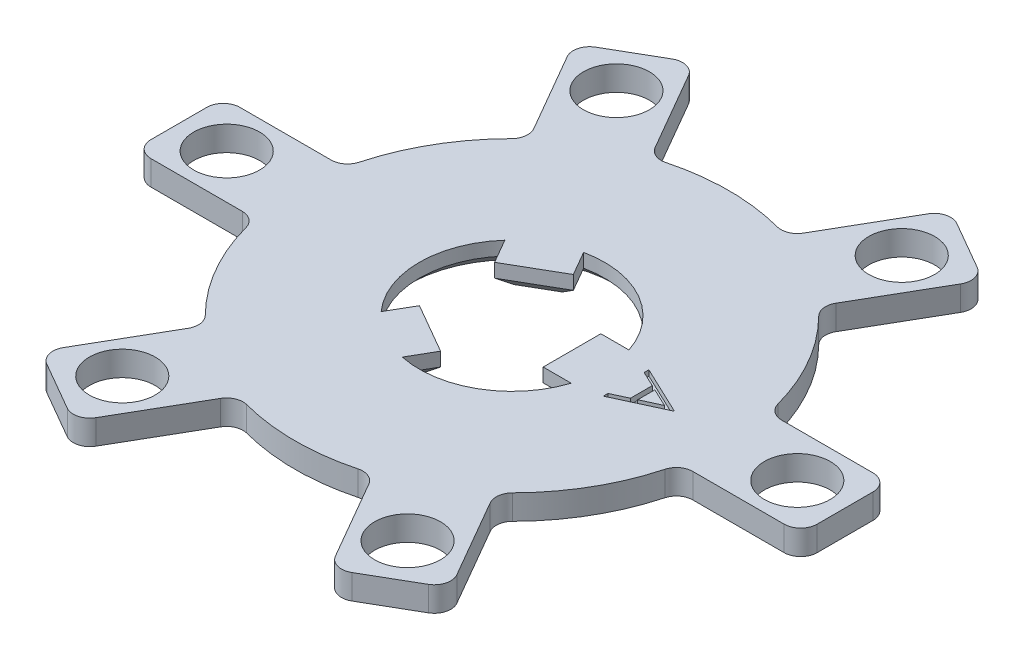
SolidWorks part; units mm, degrees
ref_plane "Front Plane" through (0, 0, 0) normal (0, 0, 1) x (1, 0, 0)
ref_plane "Top Plane" through (0, 0, 0) normal (0, 1, 0) x (1, 0, 0)
ref_plane "Right Plane" through (0, 0, 0) normal (1, 0, 0) x (0, 0, -1)
sketch "Sketch1" plane through (0, 0, 0) normal (0, 1, 0) x (1, 0, 0)
  line L0 (0, -15.8) -> (0, 15.8) construction
  line L1 (-15.8, 0) -> (0, 0) construction
  line L18 (-15.8, 0) -> (15.8, 0) construction
  line L23 (26.5479, 0) -> (-28.3106, 0) construction
  line L24 (4.9298, -15.0112) -> (9.3294, -22.6316)
  line L29 (0, 15.8) -> (0, -15.8) construction
  line L34 (15.8, 0) -> (-15.8, 0) construction
  line L35 (20.7846, 0) -> (10.3923, 18) construction
  line L36 (10.3923, 18) -> (-10.3923, 18) construction
  line L37 (-10.3923, 18) -> (-20.7846, 0) construction
  line L38 (-20.7846, 0) -> (-10.3923, -18) construction
  line L39 (-10.3923, -18) -> (10.3923, -18) construction
  line L40 (10.3923, -18) -> (20.7846, 0) construction
  line L41 (15.465, -3.2363) -> (24.2643, -3.2363)
  line L43 (15.465, 3.2363) -> (24.2643, 3.2363)
  line L44 (24.2643, -3.2363) -> (24.2643, 3.2363)
  line L45 (18, 0) -> (24.2643, 3.2363) construction
  line L46 (18, 0) -> (24.2643, -3.2363) construction
  line L47 (9.3294, -22.6316) -> (14.9349, -19.3953)
  line L48 (10.5352, -11.7749) -> (14.9349, -19.3953)
  line L49 (-10.5352, -11.7749) -> (-14.9349, -19.3953)
  line L50 (-14.9349, -19.3953) -> (-9.3294, -22.6316)
  line L51 (-4.9298, -15.0112) -> (-9.3294, -22.6316)
  line L52 (-15.465, 3.2363) -> (-24.2643, 3.2363)
  line L53 (-24.2643, 3.2363) -> (-24.2643, -3.2363)
  line L54 (-15.465, -3.2363) -> (-24.2643, -3.2363)
  line L55 (-4.9298, 15.0112) -> (-9.3294, 22.6316)
  line L56 (-9.3294, 22.6316) -> (-14.9349, 19.3953)
  line L57 (-10.5352, 11.7749) -> (-14.9349, 19.3953)
  line L58 (10.5352, 11.7749) -> (14.9349, 19.3953)
  line L59 (14.9349, 19.3953) -> (9.3294, 22.6316)
  line L60 (4.9298, 15.0112) -> (9.3294, 22.6316)
  arc A0 (15.465, 3.2363) -> (10.5352, 11.7749) centre (0, 0) ccw
  circle A1 centre (0, 0) radius 18 construction
  circle A2 centre (20.7846, 0) radius 2.4
  circle A3 centre (10.3923, -18) radius 2.4
  circle A4 centre (-10.3923, -18) radius 2.4
  circle A5 centre (-20.7846, 0) radius 2.4
  circle A6 centre (-10.3923, 18) radius 2.4
  circle A7 centre (10.3923, 18) radius 2.4
  arc A8 (10.5352, -11.7749) -> (15.465, -3.2363) centre (0, 0) ccw
  arc A9 (4.9298, 15.0112) -> (-4.9298, 15.0112) centre (0, 0) ccw
  arc A10 (-10.5352, 11.7749) -> (-15.465, 3.2363) centre (0, 0) ccw
  arc A11 (-4.9298, -15.0112) -> (4.9298, -15.0112) centre (0, 0) ccw
  arc A12 (-15.465, -3.2363) -> (-10.5352, -11.7749) centre (0, 0) ccw
  point P3 (0, 13.5)
  point P8 (18, 0)
  point P26 (0, 0)
  point P33 (0, 0)
  point P58 (0, 0)
  point P66 (0, 0)
  dimension "D1" = 4.8
  dimension "D2" = 36
  dimension "D3" = 6
  dimension "D4" = 4
extrude "Boss-Extrude1" add sketch "Sketch1" along normal blind 1.8
fillet "Fillet11" radius 1.2 24 edges at (9.3294, 0.9, 22.6316) (14.9349, 0.9, 19.3953) (10.5352, 0.9, 11.7749) (4.9298, 0.9, 15.0112) (-9.3294, 0.9, 22.6316) (-4.9298, 0.9, 15.0112) (-24.2643, 0.9, 3.2363) (-10.5352, 0.9, 11.7749) (-15.465, 0.9, 3.2363) (-14.9349, 0.9, 19.3953) (-24.2643, 0.9, -3.2363) (-15.465, 0.9, -3.2363) (-10.5352, 0.9, -11.7749) (-14.9349, 0.9, -19.3953) (-9.3294, 0.9, -22.6316) (-4.9298, 0.9, -15.0112) (4.9298, 0.9, -15.0112) (10.5352, 0.9, -11.7749) (9.3294, 0.9, -22.6316) (14.9349, 0.9, -19.3953) (15.465, 0.9, -3.2363) (24.2643, 0.9, -3.2363) (15.465, 0.9, 3.2363) (24.2643, 0.9, 3.2363)
sketch "Sketch10" plane through (0, 1.8, 0) normal (0, 1, 0) x (1, 0, 0)
  line L0 (8.3972, 2.7385) -> (8.3972, -2.9113) construction
  text T0 "A\r\n"
extrude "Cut-Extrude3" cut sketch "Sketch10" against normal offset from surface (0.4 mm away) 0.4 up to face at (-10.3923, 1.8, -15.6)
sketch "Sketch11" plane through (0, 0, 0) normal (0, 1, 0) x (1, 0, 0)
  line L0 (0, 0) -> (12.5249, 0) construction
  line L1 (-0.3675, -4.8366) -> (-4.0049, -2.7366)
  line L2 (4.3724, 2.1) -> (6.415, 2.1)
  line L3 (4.3724, 2.1) -> (4.3724, -2.1)
  line L4 (4.3724, -2.1) -> (6.415, -2.1)
  line L6 (-4.0049, -2.7366) -> (-5.0262, -4.5056)
  line L7 (-0.3675, -4.8366) -> (-1.3889, -6.6056)
  line L8 (-4.0049, 2.7366) -> (-0.3675, 4.8366)
  line L9 (-0.3675, 4.8366) -> (-1.3889, 6.6056)
  line L10 (-4.0049, 2.7366) -> (-5.0262, 4.5056)
  arc A0 (6.415, 2.1) -> (-1.3889, 6.6056) centre (0, 0) ccw
  arc A1 (-5.0262, 4.5056) -> (-5.0262, -4.5056) centre (0, 0) ccw
  arc A2 (-1.3889, -6.6056) -> (6.415, -2.1) centre (0, 0) ccw
  point P3 (7.8101, 0)
  point P20 (0, 0)
  dimension "D1" = 4.2
  dimension "D2" = 3
extrude "Cut-Extrude4" cut sketch "Sketch11" along normal mid plane 5
chamfer "Chamfer1" distance 0.8 angle 45 12 edges at (-4.5155, 0, -3.6211) (-2.1862, 0, -3.7866) (-0.8782, 0, -5.7211) (3.375, 0, -5.8457) (5.3937, 0, -2.1) (4.3724, 0, 0) (5.3937, 0, 2.1) (-6.75, 0, 0) (-4.5155, 0, 3.6211) (-2.1862, 0, 3.7866) (-0.8782, 0, 5.7211) (3.375, 0, 5.8457)
scale "Scale1" scale about centroid uniform scaling yes scale factor 1.15
